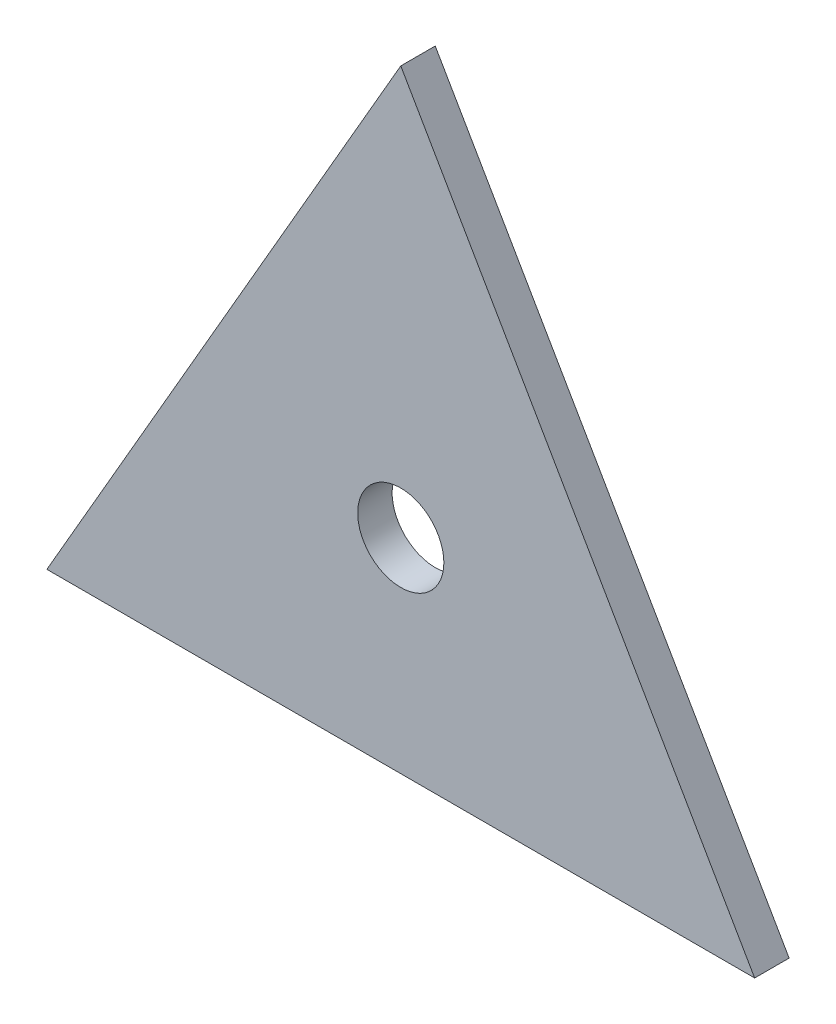
SolidWorks part; units mm, degrees
ref_plane "Front Plane" through (0, 0, 0) normal (0, 0, 1) x (1, 0, 0)
ref_plane "Top Plane" through (0, 0, 0) normal (0, 1, 0) x (1, 0, 0)
ref_plane "Right Plane" through (0, 0, 0) normal (1, 0, 0) x (0, 0, -1)
sketch "Sketch1" plane through (0, 0, 0) normal (0, 0, 1) x (1, 0, 0)
  line L0 (-282.803, 12.7) -> (-21.997, 12.7)
  line L1 (-21.997, 12.7) -> (-152.4, 238.5645)
  line L2 (-152.4, 238.5645) -> (-282.803, 12.7)
extrude "Boss-Extrude1" add sketch "Sketch1" against normal blind 12.7
sketch "Sketch2" plane through (0, 0, 0) normal (0, 0, 1) x (1, 0, 0)
  line L0 (-152.4, 238.5645) -> (-152.4, 87.9882) construction
  line L1 (-282.803, 12.7) -> (-152.4, 87.9882) construction
  line L2 (-152.4, 87.9882) -> (-21.997, 12.7) construction
  circle A0 centre (-152.4, 87.9882) radius 15.875
extrude "Cut-Extrude2" cut sketch "Sketch2" against normal blind 38.1
